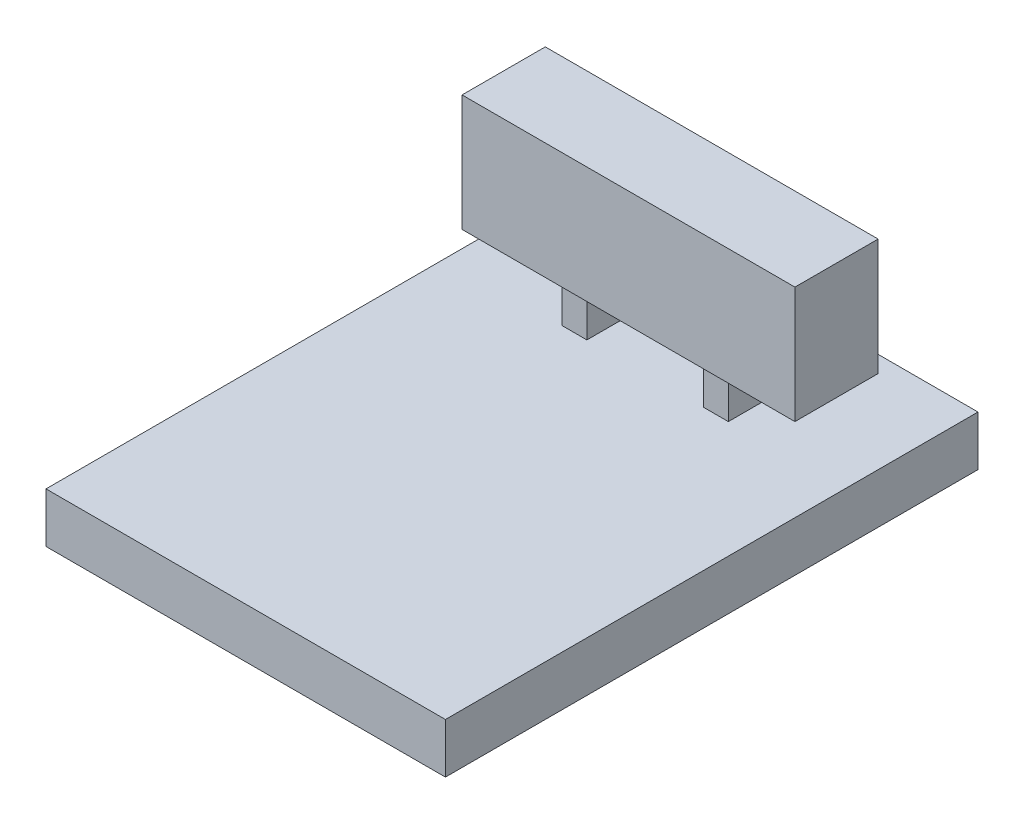
SolidWorks part; units mm, degrees
ref_plane "Front Plane" through (0, 0, 0) normal (0, 0, 1) x (1, 0, 0)
ref_plane "Top Plane" through (0, 0, 0) normal (0, 1, 0) x (1, 0, 0)
ref_plane "Right Plane" through (0, 0, 0) normal (1, 0, 0) x (0, 0, -1)
sketch "Sketch1" plane through (0, 0, 0) normal (0, 1, 0) x (1, 0, 0)
  line L1 (-22.3304, 17.6348) -> (1.6696, 17.6348)
  line L2 (-22.3304, 17.6348) -> (-22.3304, -14.3652)
  line L3 (-22.3304, -14.3652) -> (1.6696, -14.3652)
  line L4 (1.6696, 17.6348) -> (1.6696, -14.3652)
  dimension "D1" = 24
  dimension "D2" = 32
extrude "Boss-Extrude1" add sketch "Sketch1" along normal blind 3
sketch "Sketch2" plane through (0, 3, 0) normal (0, 1, 0) x (1, 0, 0)
  line L0 (1.6696, 17.6348) -> (-22.3304, 17.6348) construction
  line L1 (-15.3304, 12.6348) -> (-13.8304, 12.6348)
  line L2 (-15.3304, 12.6348) -> (-15.3304, 9.6348)
  line L3 (-15.3304, 9.6348) -> (-13.8304, 9.6348)
  line L4 (-13.8304, 12.6348) -> (-13.8304, 9.6348)
  line L5 (-6.8304, 12.6348) -> (-6.8304, 9.6348)
  line L6 (-6.8304, 12.6348) -> (-5.3304, 12.6348)
  line L7 (-5.3304, 12.6348) -> (-5.3304, 9.6348)
  line L8 (-6.8304, 9.6348) -> (-5.3304, 9.6348)
  line L9 (-22.3304, 17.6348) -> (-22.3304, -14.3652) construction
  line L10 (1.6696, -14.3652) -> (1.6696, 17.6348) construction
  dimension "D1" = 5
  dimension "D2" = 1.5
  dimension "D3" = 3
  dimension "D5" = 7
  dimension "D6" = 7
  dimension "D4" = 2
extrude "Boss-Extrude3" add sketch "Sketch2" along normal blind 3
sketch "Sketch3" plane through (0, 6, 0) normal (0, 1, 0) x (1, 0, 0)
  line L0 (1.6696, 17.6348) -> (-22.3304, 17.6348) construction
  line L1 (-20.3304, 13.6348) -> (-0.3304, 13.6348)
  line L2 (-20.3304, 13.6348) -> (-20.3304, 8.6348)
  line L3 (-20.3304, 8.6348) -> (-0.3304, 8.6348)
  line L4 (-0.3304, 13.6348) -> (-0.3304, 8.6348)
  line L5 (-22.3304, 17.6348) -> (-22.3304, -14.3652) construction
  dimension "D1" = 20
  dimension "D2" = 5
  dimension "D3" = 4
  dimension "D4" = 2
extrude "Boss-Extrude4" add sketch "Sketch3" along normal blind 7
